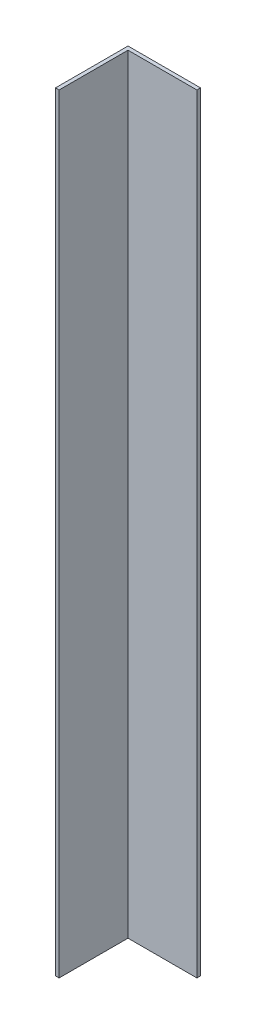
SolidWorks part; units mm, degrees
ref_plane "Plan de face" through (0, 0, 0) normal (0, 0, 1) x (1, 0, 0)
ref_plane "Plan de dessus" through (0, 0, 0) normal (0, 1, 0) x (1, 0, 0)
ref_plane "Plan de droite" through (0, 0, 0) normal (1, 0, 0) x (0, 0, -1)
sketch "Esquisse1" plane through (0, 0, 0) normal (0, 1, 0) x (1, 0, 0)
  line L1 (-20, 20.1136) -> (20, 20.1136)
  line L2 (-20, 20.1136) -> (-20, -19.8864)
  line L3 (-20, -19.8864) -> (-18, -19.8864)
  line L4 (20, 20.1136) -> (20, 18.1136)
  line L5 (-18, 18.1136) -> (20, 18.1136)
  line L6 (-18, 18.1136) -> (-18, -19.8864)
  dimension "D1" = 20
  dimension "D2" = 40
  dimension "D3" = 40
  dimension "D4" = 2
  dimension "D5" = 2
extrude "Boss.-Extru.1" add sketch "Esquisse1" along normal blind 424
